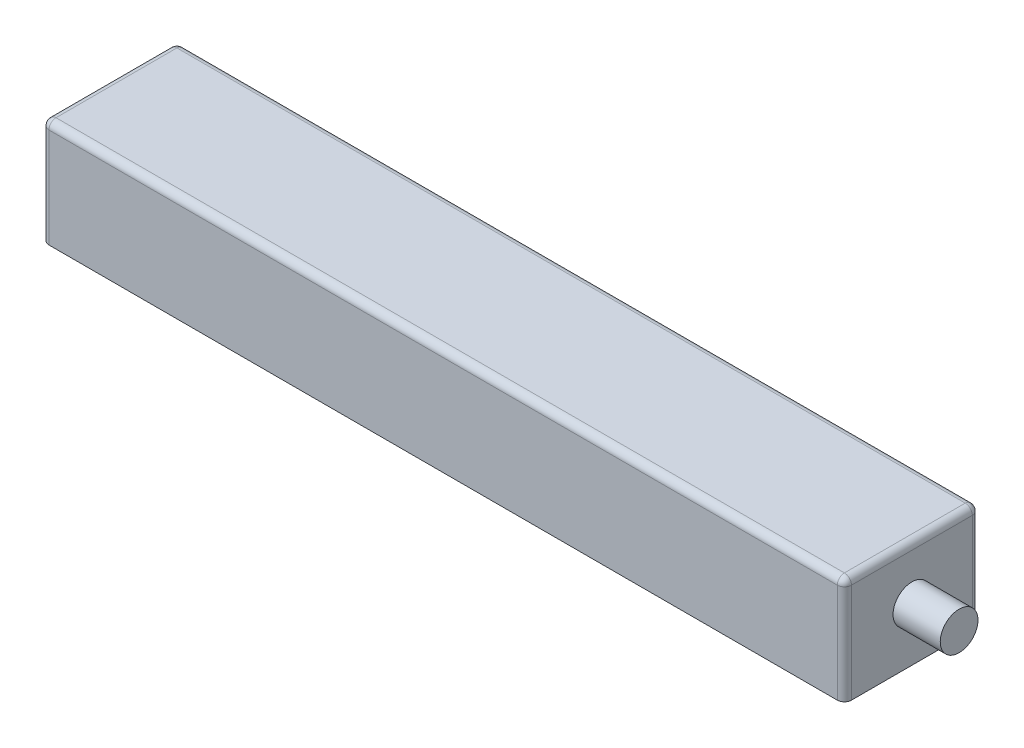
SolidWorks part; units mm, degrees
ref_plane "Front" through (0, 0, 0) normal (0, 0, 1) x (1, 0, 0)
ref_plane "Top" through (0, 0, 0) normal (0, 1, 0) x (1, 0, 0)
ref_plane "Right" through (0, 0, 0) normal (1, 0, 0) x (0, 0, -1)
sketch "Sketch1" plane through (0, 0, 0) normal (0, 1, 0) x (1, 0, 0)
  line L1 (85, -14.3) -> (-85, -14.3)
  line L2 (85, -14.3) -> (85, 14.3)
  line L3 (85, 14.3) -> (-85, 14.3)
  line L4 (-85, -14.3) -> (-85, 14.3)
  line L5 (85, -14.3) -> (-85, 14.3) construction
  line L6 (85, 14.3) -> (-85, -14.3) construction
  point P0 (0, 0)
  dimension "D1" = 170
  dimension "D2" = 28.6
extrude "Boss-Extrude1" add sketch "Sketch1" along normal blind 22.6
sketch "Sketch2" plane through (85, 0, 0) normal (1, 0, 0) x (0, 0, -1)
  line L0 (-14.3, 22.6) -> (-14.3, 0) construction
  line L2 (-14.3, 22.6) -> (14.3, 22.6) construction
  circle A0 centre (0, 11.3) radius 4
  dimension "D1" = 8
  dimension "D2" = 14.3
  dimension "D3" = 11.3
extrude "Boss-Extrude2" add sketch "Sketch2" along normal blind 10
sketch "Sketch3" plane through (-85, 0, 0) normal (-1, 0, 0) x (0, 0, 1)
  line L0 (-14.3, 22.6) -> (14.3, 22.6) construction
  line L1 (-14.3, 22.6) -> (-14.3, 0) construction
  circle A0 centre (0, 11.3) radius 4
  dimension "D1" = 8
  dimension "D2" = 11.3
  dimension "D3" = 14.3
extrude "Boss-Extrude3" add sketch "Sketch3" along normal blind 5
fillet "Fillet1" radius 1.5 8 edges at (0, 22.6, -14.3) (85, 22.6, 0) (0, 22.6, 14.3) (-85, 22.6, 0) (-85, 11.3, -14.3) (-85, 11.3, 14.3) (85, 11.3, -14.3) (85, 11.3, 14.3)
